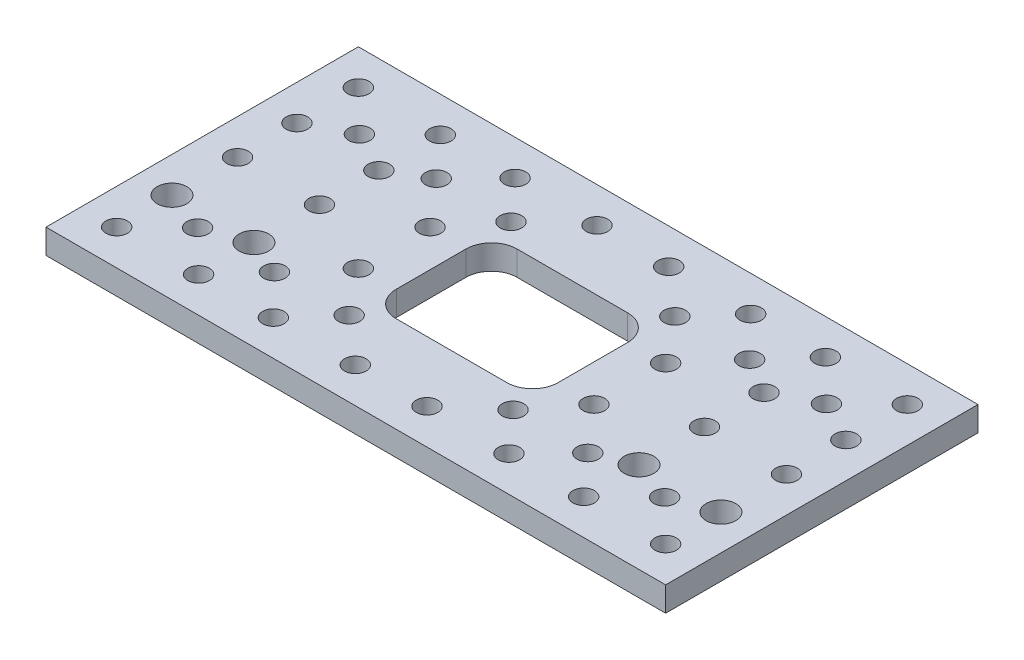
SolidWorks part; units mm, degrees
ref_plane "Front Plane" through (0, 0, 0) normal (0, 0, 1) x (1, 0, 0)
ref_plane "Top Plane" through (0, 0, 0) normal (0, 1, 0) x (1, 0, 0)
ref_plane "Right Plane" through (0, 0, 0) normal (1, 0, 0) x (0, 0, -1)
sketch "Sketch1" plane through (0, 0, 0) normal (0, 1, 0) x (1, 0, 0)
  line L0 (0, 38.735) -> (0, -38.735) construction
  line L1 (76.835, 38.735) -> (-76.835, 38.735)
  line L2 (76.835, 38.735) -> (76.835, -38.735)
  line L3 (76.835, -38.735) -> (-76.835, -38.735)
  line L4 (-76.835, 38.735) -> (-76.835, -38.735)
  line L5 (76.835, 38.735) -> (-76.835, -38.735) construction
  line L6 (76.835, -38.735) -> (-76.835, 38.735) construction
  line L7 (-57.912, 38.735) -> (-57.912, -38.735) construction
  line L8 (-76.835, 0) -> (76.835, 0) construction
  line L9 (-29.21, -6.223) -> (-29.21, 6.223) construction
  line L10 (-57.912, 17.399) -> (-57.912, -17.399) construction
  line L11 (-76.835, 38.735) -> (76.835, -38.735) construction
  line L12 (13.716, 14.986) -> (-13.716, 14.986)
  line L13 (20.066, 8.636) -> (20.066, -8.636)
  line L14 (13.716, -14.986) -> (-13.716, -14.986)
  line L15 (-20.066, 8.636) -> (-20.066, -8.636)
  line L16 (20.066, 14.986) -> (-20.066, -14.986) construction
  line L17 (20.066, -14.986) -> (-20.066, 14.986) construction
  line L18 (29.21, -6.223) -> (29.21, 6.223) construction
  line L19 (57.912, 17.399) -> (57.912, -17.399) construction
  line L20 (57.912, 38.735) -> (57.912, -38.735) construction
  circle A0 centre (-68.072, 29.972) radius 2.667
  circle A1 centre (-68.072, 14.732) radius 2.667
  circle A2 centre (-68.072, 0) radius 2.667
  circle A3 centre (-68.072, -29.972) radius 2.667
  circle A4 centre (-68.072, -16.256) radius 3.683
  circle A5 centre (-47.752, -29.972) radius 2.667
  circle A6 centre (-47.752, -16.256) radius 3.683
  circle A7 centre (-47.752, 0) radius 2.667
  circle A8 centre (-47.752, 14.732) radius 2.667
  circle A9 centre (-47.752, 29.972) radius 2.667
  circle A10 centre (-29.21, 29.972) radius 2.667
  circle A11 centre (-8.89, 29.972) radius 2.667
  circle A12 centre (-29.21, 8.89) radius 2.667
  circle A13 centre (-29.21, -8.89) radius 2.667
  circle A14 centre (-8.89, -29.972) radius 2.667
  circle A15 centre (-29.21, -29.972) radius 2.667
  circle A16 centre (-57.912, 20.066) radius 2.667
  circle A17 centre (-57.912, -20.066) radius 2.667
  arc A18 (13.716, 14.986) -> (20.066, 8.636) centre (13.716, 8.636) cw
  arc A19 (20.066, -8.636) -> (13.716, -14.986) centre (13.716, -8.636) cw
  arc A20 (-13.716, -14.986) -> (-20.066, -8.636) centre (-13.716, -8.636) cw
  arc A21 (-13.716, 14.986) -> (-20.066, 8.636) centre (-13.716, 8.636) ccw
  circle A22 centre (-20.32, 20.066) radius 2.667
  circle A23 centre (-20.32, -20.066) radius 2.667
  circle A24 centre (-38.862, 20.066) radius 2.667
  circle A25 centre (-38.862, -20.066) radius 2.667
  circle A26 centre (20.32, -20.066) radius 2.667
  circle A27 centre (8.89, -29.972) radius 2.667
  circle A28 centre (29.21, -29.972) radius 2.667
  circle A29 centre (38.862, -20.066) radius 2.667
  circle A30 centre (47.752, -29.972) radius 2.667
  circle A31 centre (68.072, -29.972) radius 2.667
  circle A32 centre (68.072, 0) radius 2.667
  circle A33 centre (68.072, -16.256) radius 3.683
  circle A34 centre (57.912, -20.066) radius 2.667
  circle A35 centre (47.752, -16.256) radius 3.683
  circle A36 centre (29.21, -8.89) radius 2.667
  circle A37 centre (29.21, 8.89) radius 2.667
  circle A38 centre (57.912, 20.066) radius 2.667
  circle A39 centre (68.072, 14.732) radius 2.667
  circle A40 centre (68.072, 29.972) radius 2.667
  circle A41 centre (47.752, 14.732) radius 2.667
  circle A42 centre (47.752, 0) radius 2.667
  circle A43 centre (38.862, 20.066) radius 2.667
  circle A44 centre (20.32, 20.066) radius 2.667
  circle A45 centre (8.89, 29.972) radius 2.667
  circle A46 centre (29.21, 29.972) radius 2.667
  circle A47 centre (47.752, 29.972) radius 2.667
  point P0 (0, 0)
  point P42 (-29.21, 0)
  point P53 (-57.912, 0)
  point P54 (0, 0)
  dimension "D3" = 5.334
  dimension "D4" = 6.096
  dimension "D5" = 6.096
  dimension "D6" = 7.366
  dimension "D7" = 6.096
  dimension "D8" = 9.906
  dimension "D9" = 9.398
  dimension "D11" = 6.223
  dimension "D12" = 26.543
  dimension "D14" = 34.798
  dimension "D17" = 6.35
  dimension "D18" = 17.653
  dimension "D19" = 36.195
  dimension "D1" = 77.47
  dimension "D2" = 153.67
  dimension "D10" = 7.493
  dimension "D13" = 12.446
  dimension "D15" = 40.132
  dimension "D16" = 29.972
extrude "Boss-Extrude1" add sketch "Sketch1" along normal blind 6.096
